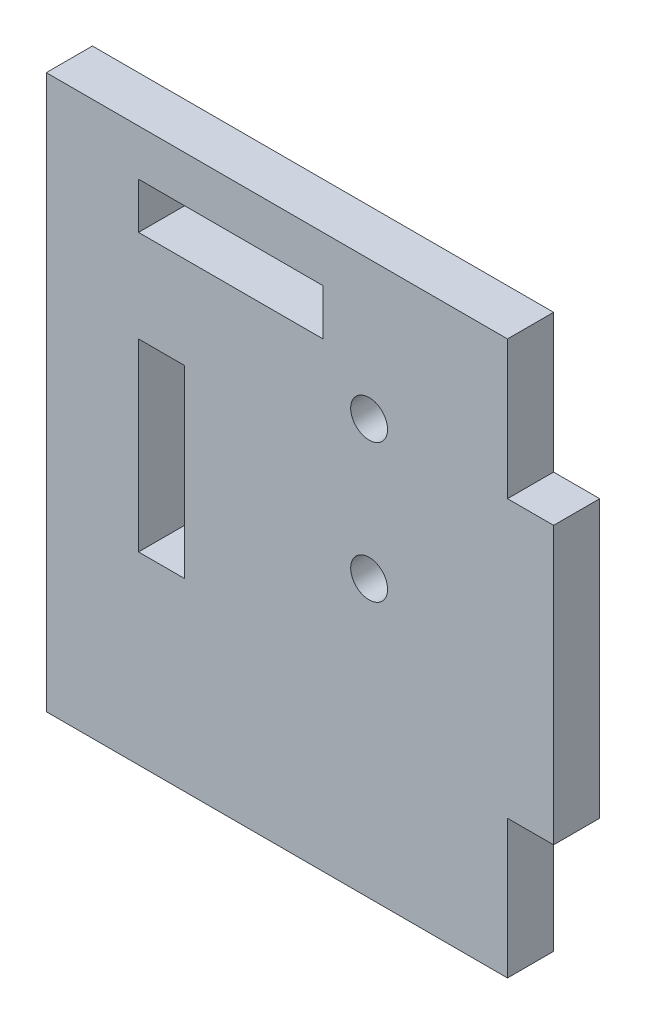
SolidWorks part; units mm, degrees
ref_plane "Plan de face" through (0, 0, 0) normal (0, 0, 1) x (1, 0, 0)
ref_plane "Plan de dessus" through (0, 0, 0) normal (0, 1, 0) x (1, 0, 0)
ref_plane "Plan de droite" through (0, 0, 0) normal (1, 0, 0) x (0, 0, -1)
sketch "Esquisse1" plane through (0, 0, 0) normal (0, 0, 1) x (1, 0, 0)
  line L0 (-55, 45) -> (-5, 45)
  line L1 (0, 0) -> (0, 30)
  line L2 (0, 0) -> (-5, 0)
  line L3 (-5, 0) -> (-5, -15)
  line L4 (-5, -15) -> (-55, -15)
  line L5 (-55, -15) -> (-55, 45)
  line L6 (0, 30) -> (-5, 30)
  line L7 (-45, 40) -> (-25, 40)
  line L8 (-45, 40) -> (-45, 35)
  line L9 (-45, 35) -> (-25, 35)
  line L10 (-25, 40) -> (-25, 35)
  line L11 (-40, 25) -> (-45, 25)
  line L12 (-40, 25) -> (-40, 5)
  line L13 (-40, 5) -> (-45, 5)
  line L14 (-45, 25) -> (-45, 5)
  line L15 (-5, 30) -> (-5, 45)
  circle A0 centre (-20, 30) radius 2
  circle A1 centre (-20, 15) radius 2
  point P15 (-45, 15)
  point P16 (-42.5, 5)
  point P23 (-30, 20.7392)
  point P24 (0, 0)
  point P25 (-30, 32.3457)
  dimension "D8" = 4
  dimension "D14" = 4
  dimension "D15" = 5
  dimension "D18" = 5
  dimension "D1" = 5
  dimension "D2" = 5
  dimension "D3" = 20
  dimension "D4" = 20
  dimension "D5" = 5
  dimension "D6" = 50
  dimension "D7" = 10
  dimension "D9" = 5
  dimension "D10" = 10
  dimension "D11" = 20
  dimension "D12" = 30
  dimension "D13" = 5
  dimension "D16" = 5
  dimension "D17" = 15
extrude "Boss.-Extru.1" add sketch "Esquisse1" along normal blind 5
